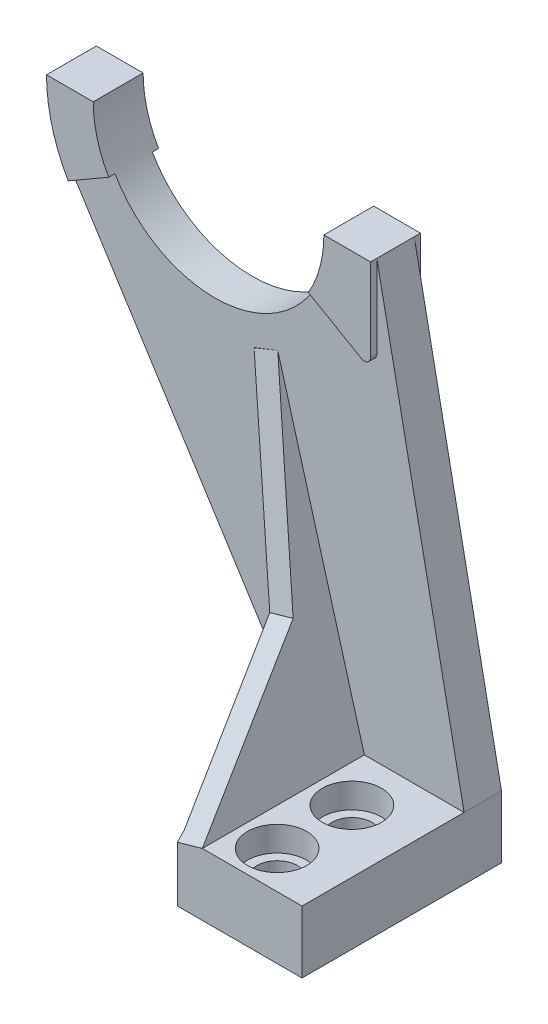
SolidWorks part; units mm, degrees
ref_plane "Alzado" through (0, 0, 0) normal (0, 0, 1) x (1, 0, 0)
ref_plane "Planta" through (0, 0, 0) normal (0, 1, 0) x (1, 0, 0)
ref_plane "Vista lateral" through (0, 0, 0) normal (1, 0, 0) x (0, 0, -1)
sketch "Croquis1" plane through (0, 0, 0) normal (0, 0, 1) x (1, 0, 0)
  line L0 (-52.3875, 63.5) -> (-40.4812, 63.5)
  line L1 (-52.3875, -63.5) -> (52.3875, -63.5) construction
  line L2 (-52.3875, -63.5) -> (-52.3875, 63.5) construction
  line L3 (-52.3875, 63.5) -> (52.3875, 63.5) construction
  line L4 (52.3875, -63.5) -> (52.3875, 63.5) construction
  line L5 (-52.3875, -63.5) -> (52.3875, 63.5) construction
  line L6 (-52.3875, 63.5) -> (52.3875, -63.5) construction
  line L7 (-40.4812, 63.5) -> (-11.1125, 63.5)
  line L8 (-11.1125, 63.5) -> (18.2563, 63.5)
  line L9 (18.2563, 63.5) -> (30.1625, 63.5)
  line L10 (30.1625, 63.5) -> (52.3875, -47.625)
  line L11 (52.3875, -47.625) -> (52.3875, -63.5)
  line L12 (52.3875, -63.5) -> (20.6375, -63.5)
  line L13 (-46.8577, 42.8625) -> (-11.1125, 63.5) construction
  line L14 (-46.8577, 42.8625) -> (20.6375, -63.5)
  arc A0 (-40.4812, 63.5) -> (18.2563, 63.5) centre (-11.1125, 63.5) ccw
  arc A1 (-52.3875, 63.5) -> (-46.8577, 42.8625) centre (-11.1125, 63.5) ccw
  arc A2 (-47.625, 63.5) -> (25.4, 63.5) centre (-11.1125, 63.5) ccw construction
  point P0 (0, 0)
  dimension "D7" = 36.5125
  dimension "D8" = 30
  dimension "D1" = 104.775
  dimension "D2" = 127
  dimension "D3" = 29.3687
  dimension "D4" = 11.9062
  dimension "D5" = 31.75
  dimension "D6" = 15.875
extrude "Saliente-Extruir1" add sketch "Croquis1" along normal blind 9.525 contours L0 A1 L14 L12 L11 L10 L9 A0
sketch "Croquis2" plane through (0, 0, 9.525) normal (0, 0, 1) x (1, 0, 0)
  line L1 (20.6375, -63.5) -> (52.3875, -63.5)
  line L2 (20.6375, -63.5) -> (20.6375, -47.625)
  line L3 (20.6375, -47.625) -> (52.3875, -47.625)
  line L4 (52.3875, -63.5) -> (52.3875, -47.625)
extrude "Saliente-Extruir2" add sketch "Croquis2" along normal blind 41.275
sketch "Croquis3" plane through (0, -47.625, 0) normal (0, 1, 0) x (1, 0, 0)
  line L0 (36.5125, -50.8) -> (36.5125, -41.275) construction
  line L1 (52.3875, -50.8) -> (20.6375, -50.8) construction
  line L2 (36.5125, -41.275) -> (36.5125, -22.225) construction
  circle A0 centre (36.5125, -41.275) radius 5.1594
  circle A1 centre (36.5125, -22.225) radius 5.1594
  dimension "D3" = 10.3187
  dimension "D1" = 9.525
  dimension "D2" = 19.05
extrude "Cortar-Extruir1" cut sketch "Croquis3" against normal through all
sketch "Croquis4" plane through (0, -47.625, 0) normal (0, 1, 0) x (1, 0, 0)
  line L0 (36.5125, -50.8) -> (36.5125, -41.275) construction
  line L1 (36.5125, -41.275) -> (36.5125, -22.225) construction
  line L2 (36.5125, -50.8) -> (36.5125, -41.275) construction
  line L3 (36.5125, -41.275) -> (36.5125, -22.225) construction
  circle A0 centre (36.5125, -22.225) radius 7.5406
  circle A1 centre (36.5125, -41.275) radius 7.5406
  dimension "D1" = 15.0812
extrude "Cortar-Extruir2" cut sketch "Croquis4" against normal blind 6.35
ref_plane "Plano1" through (0, 0, 4.7625) normal (0, 0, 1) x (1, 0, 0)
sketch "Croquis8" plane through (0, 0, 4.7625) normal (0, 0, 1) x (1, 0, 0)
  line L0 (-52.3875, 63.5) -> (-40.4812, 63.5) construction
  line L1 (18.2563, 63.5) -> (30.1625, 63.5) construction
  line L2 (-52.3875, 63.5) -> (-40.4812, 63.5)
  line L3 (18.2563, 63.5) -> (30.1625, 63.5)
  line L4 (-46.8577, 42.8625) -> (-36.5466, 48.8156)
  line L5 (-46.8577, 42.8625) -> (-11.1125, 63.5) construction
  line L6 (-11.1125, 63.5) -> (43.0374, 32.2365) construction
  line L7 (-11.1125, 63.5) -> (18.2563, 63.5) construction
  line L8 (30.1625, 63.5) -> (30.1625, 39.6699)
  line L9 (30.1625, 63.5) -> (18.2563, 63.5)
  line L10 (30.1625, 39.6699) -> (14.3216, 48.8156)
  arc A0 (-40.4812, 63.5) -> (18.2563, 63.5) centre (-11.1125, 63.5) ccw construction
  arc A1 (-52.3875, 63.5) -> (-46.8577, 42.8625) centre (-11.1125, 63.5) ccw construction
  arc A2 (-40.4812, 63.5) -> (-36.5466, 48.8156) centre (-11.1125, 63.5) ccw
  arc A3 (-52.3875, 63.5) -> (-46.8577, 42.8625) centre (-11.1125, 63.5) ccw
  arc A4 (-40.4812, 63.5) -> (-36.5466, 48.8156) centre (-11.1125, 63.5) ccw
  arc A5 (14.3216, 48.8156) -> (18.2563, 63.5) centre (-11.1125, 63.5) ccw
  dimension "D1" = 30
extrude "Saliente-Extruir5" add sketch "Croquis8" along normal mid plane 12.7 contours L2 A3 L4 A2 | A5 L10 L8 L3
fillet "Redondeo1" radius 1.5875 1 edges at (30.1625, 39.6699, 10.3188)
fillet "Redondeo4" radius 1.5875 1 edges at (30.1625, 39.6699, -0.7937)
sketch "Croquis9" plane through (0, 0, 9.525) normal (0, 0, 1) x (1, 0, 0)
  line L0 (20.6375, -47.625) -> (23.8125, -47.625) construction
  line L1 (52.3875, -47.625) -> (20.6375, -47.625) construction
  line L2 (23.8125, -47.625) -> (23.8125, 37.973) construction
  line L3 (-0.9825, 28.2533) -> (20.6375, -47.625)
  line L4 (26.9875, -47.625) -> (4.9294, 30.5708)
  line L5 (23.8125, 37.973) -> (-11.1125, 63.5) construction
  line L6 (23.8125, 37.973) -> (-34.3578, 15.1702) construction
  line L7 (23.8125, -47.625) -> (26.9875, -47.625)
  line L8 (1.9734, 29.4121) -> (-0.9825, 28.2533)
  line L9 (1.9734, 29.4121) -> (4.9294, 30.5708)
  line L18 (27.7813, 41.0447) -> (14.3216, 48.8156)
  line L19 (-36.5466, 48.8156) -> (-46.8577, 42.8625)
  line L20 (-46.8577, 42.8625) -> (20.6375, -63.5)
  line L21 (20.6375, -63.5) -> (20.6375, -47.625)
  line L22 (20.6375, -47.625) -> (52.3875, -47.625)
  line L23 (52.3875, -47.625) -> (30.1625, 63.5)
  line L24 (30.1625, 63.5) -> (30.1625, 42.4195)
  line L29 (20.6375, -47.625) -> (23.8125, -47.625)
  arc A0 (-47.625, 63.5) -> (25.4, 63.5) centre (-11.1125, 63.5) ccw construction
  arc A3 (-36.5466, 48.8156) -> (14.3216, 48.8156) centre (-11.1125, 63.5) ccw
  arc A4 (27.7813, 41.0447) -> (30.1625, 42.4195) centre (28.575, 42.4195) ccw
  dimension "D1" = 3.175
  dimension "D2" = 85.598
  dimension "D3" = 3.175
  dimension "D4" = 3.175
  dimension "D5" = 0
extrude "Saliente-Extruir8" add sketch "Croquis9" along normal blind 41.275
sketch "Croquis12" plane through (12.5541, 3.5414, 0) normal (0.9624, 0.2715, 0) x (0, 0, -1)
  line L0 (-9.525, -21.4131) -> (-19.05, -21.4131) construction
  line L1 (-9.525, 52.9261) -> (-9.525, -60.059) construction
  line L2 (-9.525, 28.0843) -> (-50.8, 28.0843)
  line L3 (-50.8, 28.0843) -> (-50.8, -53.1631)
  line L4 (-19.05, -21.4131) -> (-19.05, -53.1631) construction
  line L6 (-50.8, -53.1631) -> (-9.525, -53.1631) construction
  line L8 (-50.8, -53.1631) -> (-19.05, -21.4131)
  line L9 (-19.05, -21.4131) -> (-9.525, 28.0843)
  dimension "D1" = 31.75
  dimension "D2" = 9.525
extrude "Cortar-Extruir4" cut sketch "Croquis12" against normal blind 41.275
